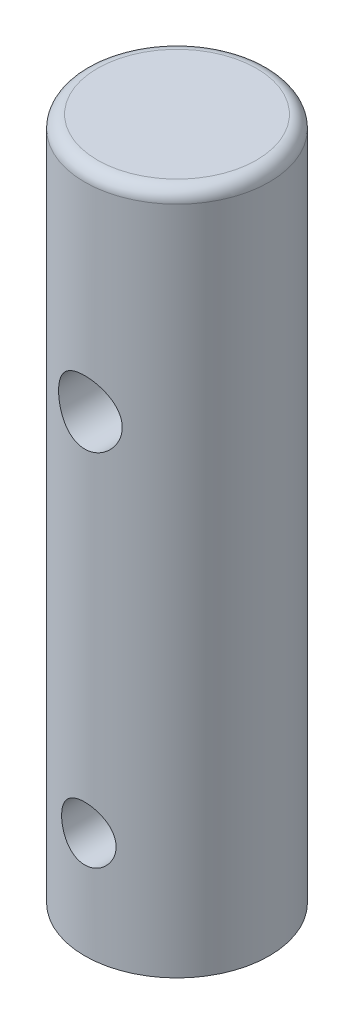
SolidWorks part; units mm, degrees
material "6061-T6 (SS)"
ref_plane "Front Plane" through (0, 0, 0) normal (0, 0, 1) x (1, 0, 0)
ref_plane "Top Plane" through (0, 0, 0) normal (0, 1, 0) x (1, 0, 0)
ref_plane "Right Plane" through (0, 0, 0) normal (1, 0, 0) x (0, 0, -1)
sketch "Sketch1" plane through (0, 0, 0) normal (0, 1, 0) x (1, 0, 0)
  circle A0 centre (0, 0) radius 5.5245
  dimension "D1" = 11.049
extrude "Boss-Extrude1" add sketch "Sketch1" along normal blind 40.894
sketch "Sketch2" plane through (0, 0, 0) normal (0, 0, 1) x (1, 0, 0)
  line L0 (5.5245, 40.894) -> (-5.5245, 40.894) construction
  line L1 (-5.5245, 0) -> (5.5245, 0) construction
  circle A0 centre (0, 28.194) radius 1.905
  circle A1 centre (0, 6.35) radius 1.632
  dimension "D3" = 3.81
  dimension "D4" = 3.2639
  dimension "D1" = 12.7
  dimension "D2" = 6.35
extrude "Cut-Extrude1" cut sketch "Sketch2" against normal through all both and the other way through all
fillet "Fillet1" radius 0.762 1 edges at (0, 40.894, 5.5245)
